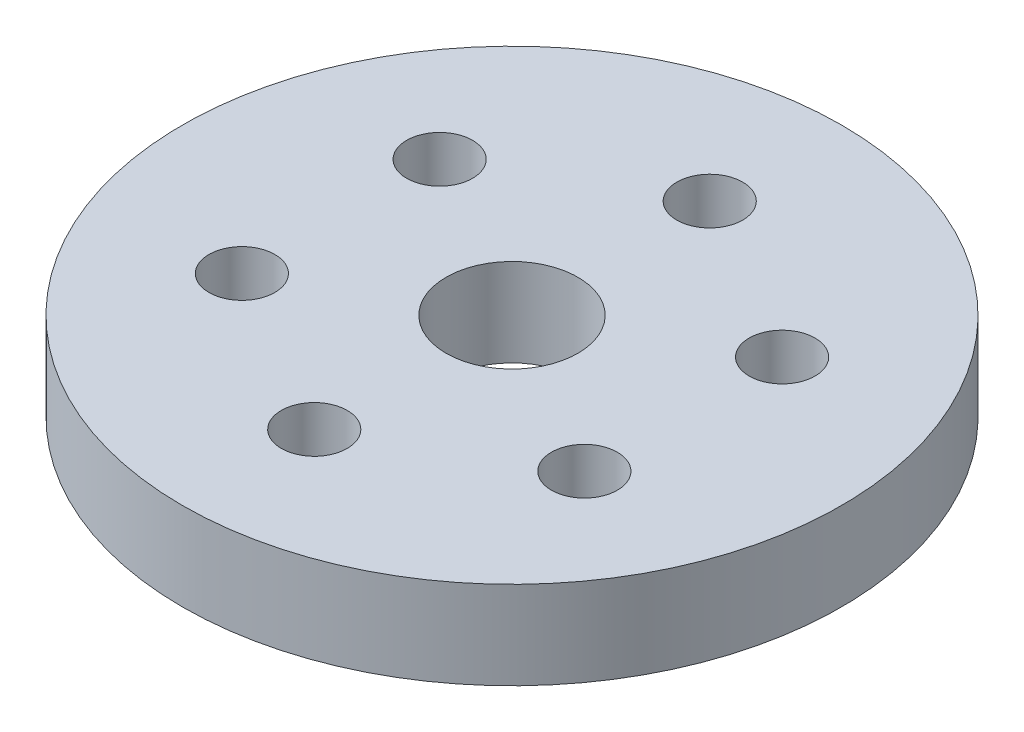
SolidWorks part; units mm, degrees
material "Balsa"
ref_plane "Front Plane" through (0, 0, 0) normal (0, 0, 1) x (1, 0, 0)
ref_plane "Top Plane" through (0, 0, 0) normal (0, 1, 0) x (1, 0, 0)
ref_plane "Right Plane" through (0, 0, 0) normal (1, 0, 0) x (0, 0, -1)
sketch "Sketch1" plane through (0, 0, 0) normal (0, 1, 0) x (1, 0, 0)
  circle A0 centre (0, 0) radius 15.875
  circle A1 centre (0, 0) radius 3.175
  dimension "D1" = 31.75
  dimension "D2" = 6.35
extrude "Boss-Extrude1" add sketch "Sketch1" along normal mid plane 4.2333
sketch "Sketch2" plane through (0, 0, 0) normal (0, 1, 0) x (1, 0, 0)
  line L0 (0, 3.175) -> (0, 15.875) construction
  circle A0 centre (0, 9.525) radius 1.5875
  circle A1 centre (0, 0) radius 3.175 construction
  circle A2 centre (0, 0) radius 15.875 construction
  circle A3 centre (8.2489, 4.7625) radius 1.5875
  circle A4 centre (8.2489, -4.7625) radius 1.5875
  circle A5 centre (0, -9.525) radius 1.5875
  circle A6 centre (-8.2489, -4.7625) radius 1.5875
  circle A7 centre (-8.2489, 4.7625) radius 1.5875
  point P9 (0, 9.525)
  point P23 (0, 0)
  dimension "D1" = 3.175
  dimension "D2" = 6
extrude "Cut-Extrude1" cut sketch "Sketch2" against normal through all and the other way through all
